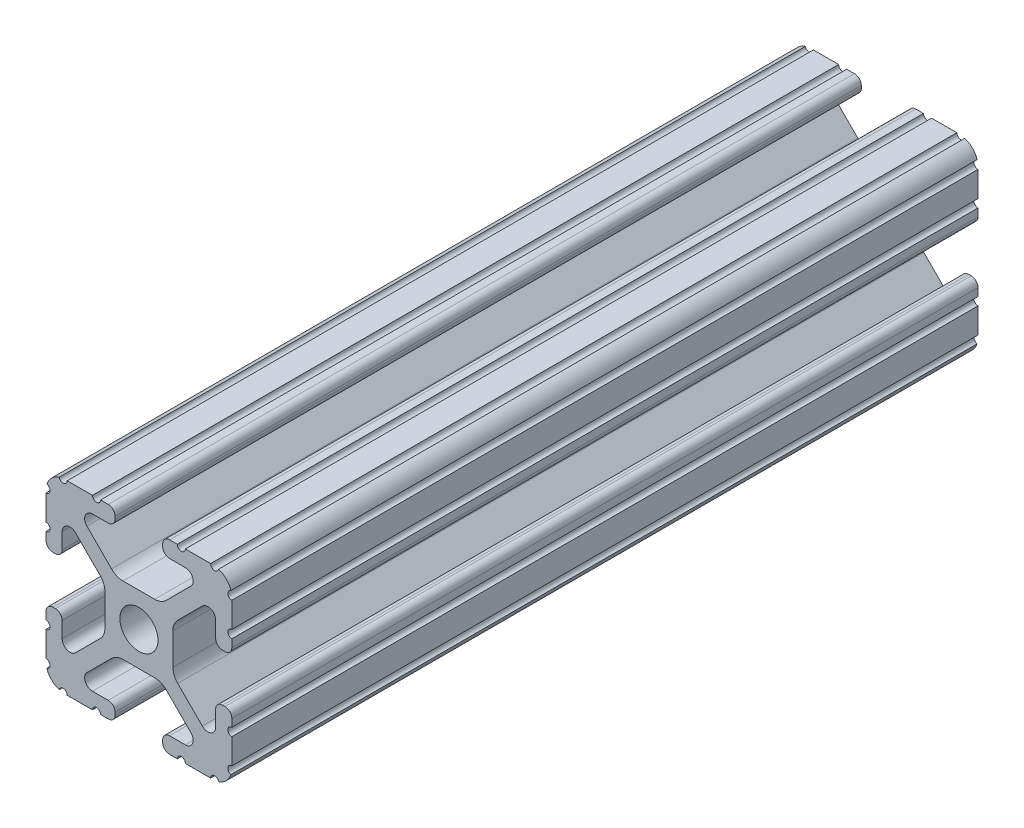
SolidWorks part; units mm, degrees
ref_plane "Front Plane" through (0, 0, 0) normal (0, 0, 1) x (1, 0, 0)
ref_plane "Top Plane" through (0, 0, 0) normal (0, 1, 0) x (1, 0, 0)
ref_plane "Right Plane" through (0, 0, 0) normal (1, 0, 0) x (0, 0, -1)
sketch "Sketch2" plane through (0, 0, 0) normal (0, 0, 1) x (1, 0, 0)
  line L0 (0, 12.7) -> (0, -12.7) construction
  line L1 (-12.7, 0) -> (12.7, 0) construction
  line L2 (3.2512, -12.7) -> (12.7, -12.7)
  line L3 (12.7, -12.7) -> (12.7, -3.2512)
  line L4 (3.2512, -12.7) -> (3.2512, -10.4902)
  line L5 (3.2512, -10.4902) -> (8.9276, -10.4902)
  line L6 (8.9276, -10.4902) -> (3.0856, -4.6482)
  line L7 (0, 0) -> (12.7, -12.7) construction
  line L8 (12.7, -3.2512) -> (10.4902, -3.2512)
  line L9 (10.4902, -3.2512) -> (10.4902, -8.9276)
  line L10 (10.4902, -8.9276) -> (4.6482, -3.0856)
  circle A0 centre (0, 0) radius 2.6035
  arc A1 (6.3485, -10.4902) -> (7.1039, -8.6665) centre (6.3485, -9.4219) ccw construction
  point P8 (0, -4.6482)
  dimension "Center Hole Diameter" = 5.207
  dimension "Rail Height" = 25.4
  dimension "Rail Width" = 25.4
  dimension "T-Slot Width" = 6.5024
  dimension "Slot Inner Width" = 14.8336
  dimension "Thickness" = 2.2098
  dimension "Slot Depth" = 5.842
  dimension "D1" = 2.2098
sketch "Sketch3" plane through (0, 0, 0) normal (1, 0, 0) x (0, 0, -1)
  line L0 (-76.2, -12.7) -> (76.2, -12.7) construction
  line L1 (-68.58, 0) -> (68.58, 0) construction
  dimension "Length" = 152.4
  dimension "D1" = 137.16
sketch "Sketch4" plane through (0, 0, 0) normal (0, 0, 1) x (1, 0, 0)
  line L0 (4.1904, -12.7) -> (10.1173, -12.7)
  line L1 (3.2512, -12.7) -> (12.7, -12.7) construction
  line L2 (3.2512, -12.7) -> (3.2512, -10.4902) construction
  line L3 (3.2512, -10.4902) -> (8.9276, -10.4902) construction
  line L4 (3.2512, -11.4294) -> (3.2512, -11.7608)
  line L5 (4.1904, -10.4902) -> (6.3485, -10.4902)
  line L6 (0, -4.6482) -> (2.164, -4.6482)
  line L7 (8.9276, -10.4902) -> (3.0856, -4.6482) construction
  line L8 (3.7373, -5.2999) -> (7.1039, -8.6665)
  line L9 (12.7, -12.7) -> (12.7, -3.2512) construction
  line L10 (10.4902, -8.9276) -> (4.6482, -3.0856) construction
  line L11 (10.4902, -3.2512) -> (10.4902, -8.9276) construction
  line L12 (10.4902, -6.3485) -> (10.4902, -4.1904)
  line L13 (12.7, -3.2512) -> (10.4902, -3.2512) construction
  line L14 (11.4294, -3.2512) -> (11.7608, -3.2512)
  line L15 (12.7, -4.1904) -> (12.7, -10.1173)
  line L16 (8.6665, -7.1039) -> (5.2999, -3.7373)
  line L17 (4.6482, 0) -> (4.6482, -2.164)
  line L18 (-12.7, 0) -> (12.7, 0) construction
  line L19 (0, -4.6482) -> (0, -2.6035)
  line L20 (0, 12.7) -> (0, -12.7) construction
  line L21 (4.6482, 0) -> (2.6035, 0)
  arc A0 (3.2512, -11.7608) -> (4.1904, -12.7) centre (4.1904, -11.7608) ccw
  arc A2 (3.2512, -11.4294) -> (4.1904, -10.4902) centre (4.1904, -11.4294) cw
  arc A3 (6.3485, -10.4902) -> (7.1039, -8.6665) centre (6.3485, -9.4219) ccw
  arc A4 (2.164, -4.6482) -> (3.7373, -5.2999) centre (2.164, -6.8732) cw
  arc A5 (10.1173, -12.7) -> (12.7, -10.1173) centre (10.1173, -10.1173) ccw
  arc A6 (8.6665, -7.1039) -> (10.4902, -6.3485) centre (9.4219, -6.3485) ccw
  arc A7 (10.4902, -4.1904) -> (11.4294, -3.2512) centre (11.4294, -4.1904) cw
  arc A8 (11.7608, -3.2512) -> (12.7, -4.1904) centre (11.7608, -4.1904) cw
  arc A9 (5.2999, -3.7373) -> (4.6482, -2.164) centre (6.8732, -2.164) cw
  circle A10 centre (0, 0) radius 2.6035 construction
  arc A11 (0, -2.6035) -> (2.6035, 0) centre (0, 0) ccw
  dimension "D1" = 2.5827
  dimension "D2" = 2.225
  dimension "D3" = 0.9392
extrude "Boss-Extrude1" add sketch "Sketch4" along normal mid plane 102.0001
sketch "Sketch5" plane through (0, 0, 0) normal (0, 0, 1) x (1, 0, 0)
  line L0 (3.2512, -12.7) -> (12.7, -12.7) construction
  line L1 (4.1904, -10.4902) -> (6.3485, -10.4902) construction
  line L3 (0, 0) -> (12.7, -12.7) construction
  line L4 (6.3485, -10.4902) -> (6.3485, -12.7) construction
  line L5 (8.9276, -10.4902) -> (3.0856, -4.6482) construction
  circle A0 centre (10.3562, -12.7) radius 0.5524
  circle A1 centre (5.796, -12.7) radius 0.5524
  circle A2 centre (12.7, -10.3562) radius 0.5524
  circle A3 centre (12.7, -5.796) radius 0.5524
  point P10 (5.2694, -10.4902)
  point P12 (9.4219, -6.3485)
  dimension "D1" = 1.1049
extrude "Cut-Extrude1" cut sketch "Sketch5" against normal through all both and the other way through all
mirror "Mirror1" about plane through (0, 0, 0) normal (1, 0, 0) of bodies 137 134
mirror "Mirror2" about plane through (0, 0, 0) normal (0, 1, 0) of bodies 135
equation "\"D1@Boss-Extrude1\"=4.01575"
equation "\"D1@Sketch2\"=\"Thickness@Sketch2\""
equation "\"D2@Sketch4\"=\"Slot Inner Width@Sketch2\"*0.15"
equation "\"D1@Sketch4\"=\"D3@Sketch4\"*2.75"
equation "\"D3@Sketch4\"=\"Thickness@Sketch2\"*0.425"
equation "\"D1@Sketch5\"=\"Thickness@Sketch2\"*0.5"
equation "\"D1@Sketch3\"=\"Length@Sketch3\"*0.9"
